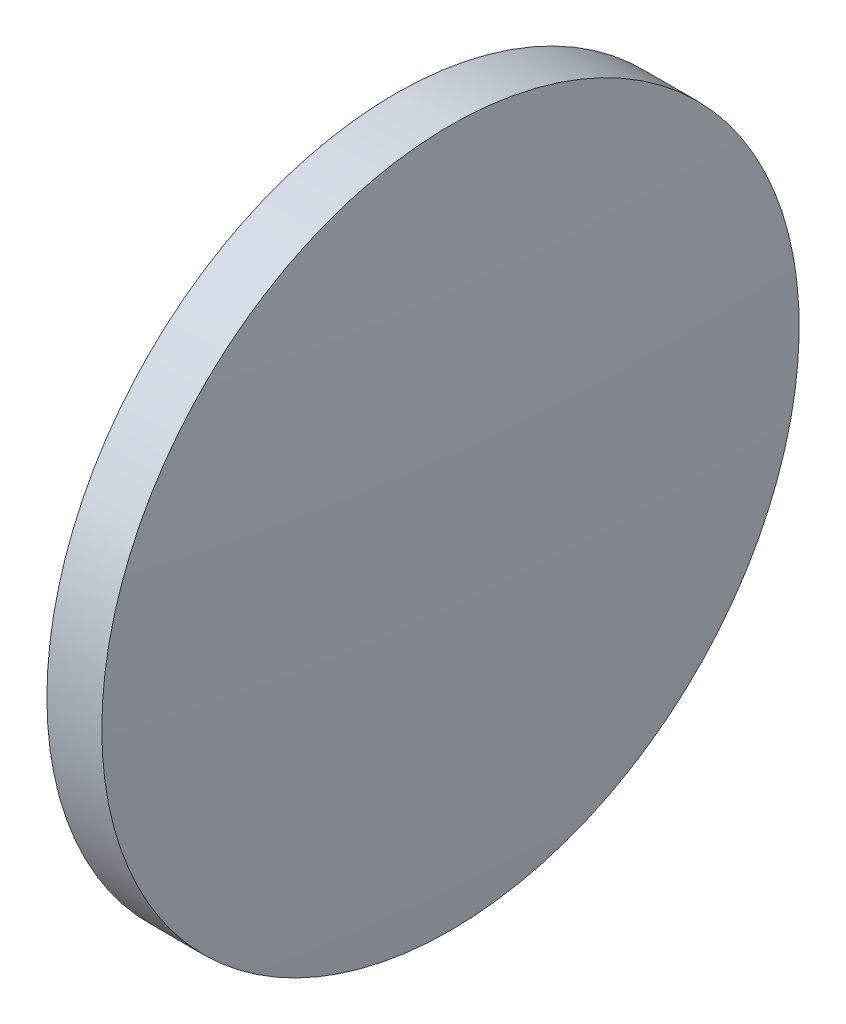
SolidWorks part; units mm, degrees
ref_plane "前视基准面" through (0, 0, 0) normal (0, 0, 1) x (1, 0, 0)
ref_plane "上视基准面" through (0, 0, 0) normal (0, 1, 0) x (1, 0, 0)
ref_plane "右视基准面" through (0, 0, 0) normal (1, 0, 0) x (0, 0, -1)
sketch "草图1" plane through (0, 0, 0) normal (0, 0, 1) x (1, 0, 0)
  line L0 (79.3054, 48.6161) -> (93.4772, 48.6161) construction
  line L1 (85.4585, 61.3161) -> (87.4579, 61.3161)
  line L2 (87.4579, 61.3161) -> (87.4579, 35.9161)
  line L3 (87.4579, 35.9161) -> (85.4585, 35.9161)
  line L4 (85.4585, 35.9161) -> (85.4585, 61.3161)
  arc A0 (85.4585, 61.3161) -> (85.4585, 35.9161) centre (264.3228, 48.6161) ccw
  arc A1 (87.4579, 35.9161) -> (87.4579, 61.3161) centre (-91.4064, 48.6161) ccw
  dimension "D1" = 25.4
  dimension "D2" = 1.9993
revolve "旋转1" add sketch "草图1" angle 360 about L0
